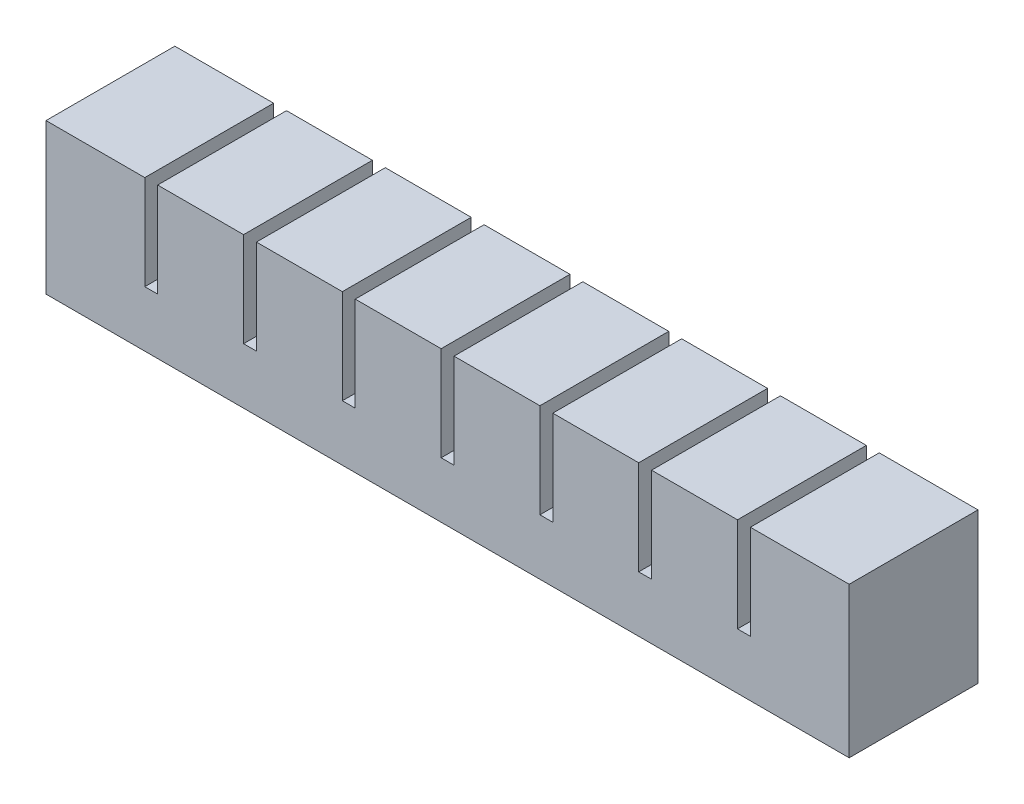
SolidWorks part; units mm, degrees
ref_plane "Front Plane" through (0, 0, 0) normal (0, 0, 1) x (1, 0, 0)
ref_plane "Top Plane" through (0, 0, 0) normal (0, 1, 0) x (1, 0, 0)
ref_plane "Right Plane" through (0, 0, 0) normal (1, 0, 0) x (0, 0, -1)
sketch "Sketch1" plane through (0, 0, 0) normal (0, 0, 1) x (1, 0, 0)
  line L1 (0, 0) -> (20, 0)
  line L2 (0, 0) -> (0, 30)
  line L3 (0, 30) -> (20, 30)
  line L4 (20, 0) -> (20, 30)
  dimension "D1" = 20
  dimension "D2" = 30
extrude "Boss-Extrude1" add sketch "Sketch1" along normal blind 30
sketch "Sketch2" plane through (0, 0, 0) normal (0, -1, 0) x (1, 0, 0)
  line L0 (20, 30) -> (20, 0) construction
  line L1 (5, 25) -> (15, 25)
  line L2 (5, 25) -> (5, 5)
  line L3 (5, 5) -> (15, 5)
  line L4 (15, 25) -> (15, 5)
  line L5 (0, 30) -> (0, 0) construction
  line L6 (0, 30) -> (20, 30) construction
  line L7 (0, 0) -> (20, 0) construction
  dimension "D1" = 5
  dimension "D2" = 5
  dimension "D3" = 5
  dimension "D4" = 5
extrude "Cut-Extrude1" cut sketch "Sketch2" against normal blind 25
sketch "Sketch3" plane through (20, 0, 0) normal (1, 0, 0) x (0, 0, -1)
  line L0 (0, 0) -> (0, 30) construction
  line L1 (-30, 0) -> (0, 0)
  line L2 (-30, 0) -> (-30, 8)
  line L3 (-30, 8) -> (0, 8)
  line L4 (0, 0) -> (0, 8)
  dimension "D1" = 8
extrude "Boss-Extrude2" add sketch "Sketch3" along normal blind 3
pattern_linear "LPattern1" count 8 spacing 23 along (1, 0, 0) of bodies 103
combine bodies "Combine1" operation type add bodies to combine 110 103 104 105 106 107 108 109
sketch "Sketch4" plane through (181, 0, 0) normal (1, 0, 0) x (0, 0, -1)
  line L1 (-30, 30) -> (0, 30)
  line L2 (-30, 30) -> (-30, 8)
  line L3 (-30, 8) -> (0, 8)
  line L4 (0, 30) -> (0, 8)
extrude "Boss-Extrude3" add sketch "Sketch4" along normal up to surface (3 mm away) up to face at (184, 4, 15)
sketch "Sketch5" plane through (0, 0, 0) normal (-1, 0, 0) x (0, 0, 1)
  line L1 (0, 30) -> (30, 30)
  line L2 (0, 30) -> (0, 0)
  line L3 (0, 0) -> (30, 0)
  line L4 (30, 30) -> (30, 0)
extrude "Boss-Extrude4" add sketch "Sketch5" along normal blind 3
ref_point "Point1"
sketch "Sketch6" plane through (0, 0, 0) normal (0, -1, 0) x (1, 0, 0)
  line L0 (166, 25) -> (166, 5) construction
  line L1 (15, 16.5) -> (166, 16.5)
  line L2 (15, 16.5) -> (15, 13.5)
  line L3 (15, 13.5) -> (166, 13.5)
  line L4 (166, 16.5) -> (166, 13.5)
  line L5 (15, 16.5) -> (166, 13.5) construction
  line L6 (15, 13.5) -> (166, 16.5) construction
  point P0 (90.5, 15)
  dimension "D1" = 3
extrude "Cut-Extrude2" cut sketch "Sketch6" against normal blind 3
sketch "Sketch7" plane through (0, 0, 0) normal (0, -1, 0) x (1, 0, 0)
  line L0 (-3, 0) -> (184, 0) construction
  line L1 (-3, 30) -> (184, 30)
  line L2 (-3, 30) -> (-3, 0)
  line L3 (-3, 0) -> (184, 0)
  line L4 (184, 30) -> (184, 0)
extrude "Boss-Extrude5" add sketch "Sketch7" along normal blind 5
